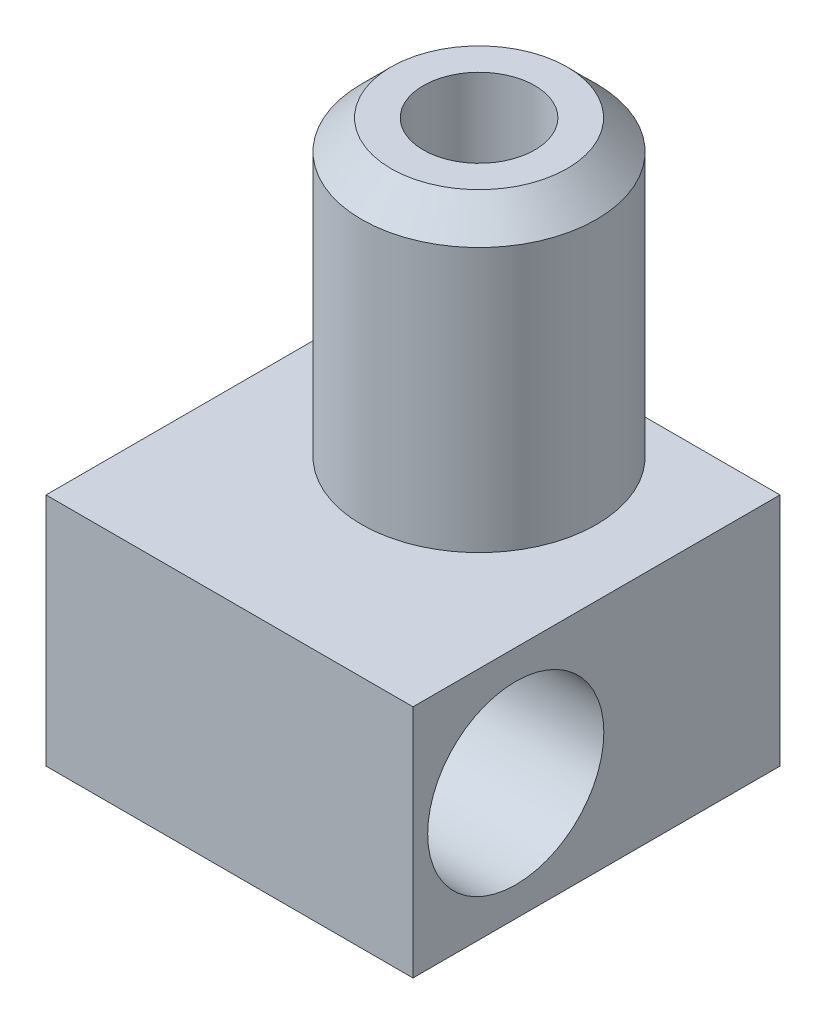
SolidWorks part; units mm, degrees
material "Ottone"
ref_plane "Piano frontale" through (0, 0, 0) normal (0, 0, 1) x (1, 0, 0)
ref_plane "Piano superiore" through (0, 0, 0) normal (0, 1, 0) x (1, 0, 0)
ref_plane "Piano destro" through (0, 0, 0) normal (1, 0, 0) x (0, 0, -1)
sketch "Schizzo1" plane through (0, 0, 0) normal (0, 0, 1) x (1, 0, 0)
  line L0 (-0.15, 0) -> (-0.15, -3)
  line L1 (-0.15, -3) -> (-0.5, -3)
  line L2 (-0.5, -3) -> (-4, -1)
  line L3 (-4, -1) -> (-4, 0)
  line L4 (-4, 0) -> (-0.15, 0)
  line L5 (0, -26.5282) -> (0, 14.9614) construction
  dimension "D1" = 0.3
  dimension "D2" = 3
  dimension "D3" = 8
  dimension "D4" = 1
  dimension "D5" = 1
revolve "Rivoluzione1" add sketch "Schizzo1" angle 360 about L5
sketch "Schizzo2" plane through (0, 0, 0) normal (0, 1, 0) x (1, 0, 0)
  line L0 (0, 0) -> (0, -10.5487) construction
  line L1 (-6.25, -8.5) -> (6.25, -8.5)
  line L2 (-6.25, -8.5) -> (-6.25, 4)
  line L3 (-6.25, 4) -> (6.25, 4)
  line L4 (6.25, -8.5) -> (6.25, 4)
  circle A0 centre (0, 0) radius 4 construction
  circle A1 centre (0, 0) radius 0.15 construction
  circle A2 centre (0, 0) radius 0.15
  dimension "D1" = 12.5
extrude "Estrusione-Estrusione1" add sketch "Schizzo2" along normal blind 8
sketch "Schizzo3" plane through (6.25, 0, 0) normal (1, 0, 0) x (0, 0, -1)
  line L0 (-5, 4) -> (-5.859, 4) construction
  line L1 (-8.5, 8) -> (4, 8) construction
  line L2 (-8.5, 0) -> (4, 0) construction
  line L3 (-8.5, 8) -> (-8.5, 0) construction
  circle A0 centre (-5, 4) radius 3
  dimension "D1" = 0.5
  dimension "D2" = 6
extrude "Taglio-Estrusione1" cut sketch "Schizzo3" against normal through all
sketch "Schizzo4" plane through (0, 0, -4) normal (0, 0, -1) x (-1, 0, 0)
  line L0 (-6.25, 8) -> (-6.25, 0) construction
  line L1 (-5.3, 4) -> (-4.0807, 4) construction
  line L2 (-6.25, 8) -> (6.25, 8) construction
  line L3 (-6.25, 0) -> (0, 0) construction
  circle A0 centre (-5.3, 4) radius 0.75
  dimension "D1" = 1.5
  dimension "D2" = 0.2
extrude "Taglio-Estrusione2" cut sketch "Schizzo4" against normal blind 3.5
sketch "Schizzo5" plane through (0, 8, 0) normal (0, 1, 0) x (1, 0, 0)
  circle A0 centre (0, 0) radius 4
  dimension "D1" = 8
extrude "Estrusione-Estrusione2" add sketch "Schizzo5" along normal blind 10
cosmetic thread "Filettatura cosmetica1" parameters "D2"=6.891
chamfer "Smusso1" distance 1 angle 45 1 edges at (0, 18, 4)
hole_wizard "Foro Ø3.8 (3.8)-1" positions "Schizzo7" profile "Schizzo6" hole size "Ø3.8" standard "ISO"
sketch "Schizzo7" plane through (0, 18, 0) normal (0, 1, 0) x (1, 0, 0)
  point P0 (0, 0)
sketch "Schizzo6" plane through (0, 18, 0) normal (1, 0, 0) x (0, 0, 1)
  line L0 (0, 0) -> (0, 16.1416)
  line L1 (0, 16.1416) -> (1.9, 15)
  line L2 (1.9, 15) -> (1.9, 0)
  line L5 (1.9, 0) -> (0, 0)
  line L10 (0, 16.1416) -> (-1.9, 15) construction
  line L11 (0, -6.35) -> (0, 107.95) construction
  dimension "Hole Dia." = 3.8
  dimension "Hole Depth" = 15
  dimension "Drill Angle" = 118
